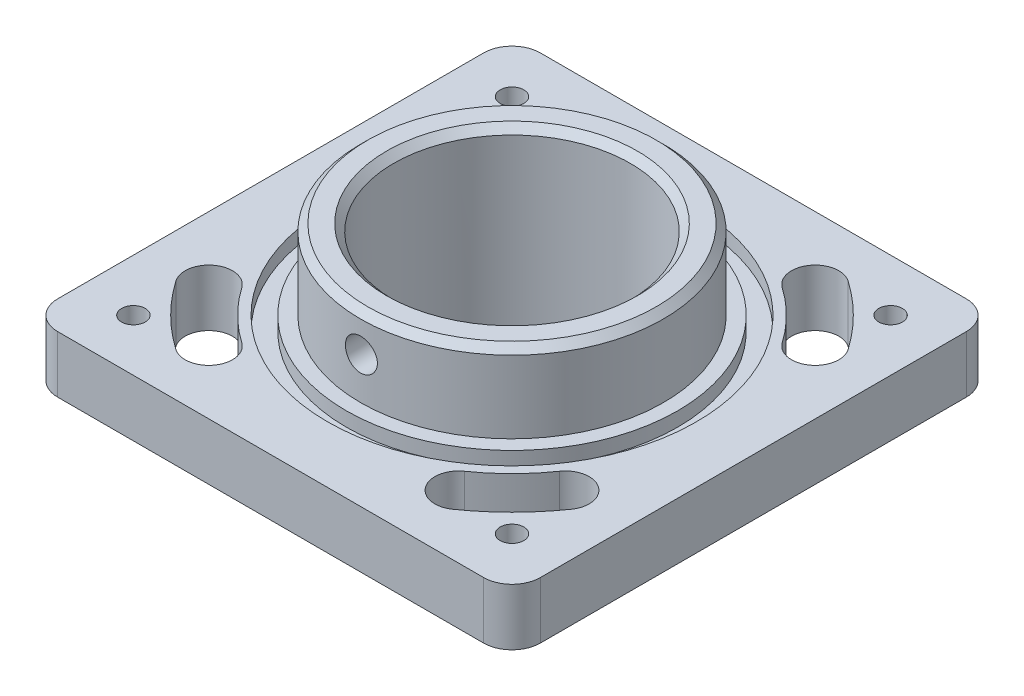
SolidWorks part; units mm, degrees
ref_plane "Face" through (0, 0, 0) normal (0, 0, 1) x (1, 0, 0)
ref_plane "Dessus" through (0, 0, 0) normal (0, 1, 0) x (1, 0, 0)
ref_plane "Droite" through (0, 0, 0) normal (1, 0, 0) x (0, 0, -1)
sketch "Esquisse1" plane through (0, 0, 0) normal (0, 1, 0) x (1, 0, 0)
  line L0 (-59.8186, 41.8854) -> (0, 0) construction
  line L1 (-80.9625, -80.9625) -> (80.9625, -80.9625)
  line L2 (-80.9625, -80.9625) -> (-80.9625, 80.9625)
  line L3 (-80.9625, 80.9625) -> (80.9625, 80.9625)
  line L4 (80.9625, -80.9625) -> (80.9625, 80.9625)
  line L5 (-80.9625, -80.9625) -> (80.9625, 80.9625) construction
  line L6 (-80.9625, 80.9625) -> (80.9625, -80.9625) construction
  line L7 (0, 0) -> (-41.8854, 59.8186) construction
  circle A0 centre (0, 0) radius 39.6875
  arc A1 (-41.8854, 59.8186) -> (-59.8186, 41.8854) centre (0, 0) ccw construction
  arc A2 (-46.4382, 66.3206) -> (-66.3206, 46.4382) centre (0, 0) ccw
  arc A3 (-37.3327, 53.3166) -> (-53.3166, 37.3327) centre (0, 0) ccw
  arc A4 (-37.3327, 53.3166) -> (-46.4382, 66.3206) centre (-41.8854, 59.8186) ccw
  arc A5 (-66.3206, 46.4382) -> (-53.3166, 37.3327) centre (-59.8186, 41.8854) ccw
  arc A6 (59.8186, 41.8854) -> (41.8854, 59.8186) centre (0, 0) ccw construction
  arc A7 (66.3206, 46.4382) -> (46.4382, 66.3206) centre (0, 0) ccw
  arc A8 (53.3166, 37.3327) -> (37.3327, 53.3166) centre (0, 0) ccw
  arc A9 (53.3166, 37.3327) -> (66.3206, 46.4382) centre (59.8186, 41.8854) ccw
  arc A10 (46.4382, 66.3206) -> (37.3327, 53.3166) centre (41.8854, 59.8186) ccw
  arc A11 (41.8854, -59.8186) -> (59.8186, -41.8854) centre (0, 0) ccw construction
  arc A12 (46.4382, -66.3206) -> (66.3206, -46.4382) centre (0, 0) ccw
  arc A13 (37.3327, -53.3166) -> (53.3166, -37.3327) centre (0, 0) ccw
  arc A14 (37.3327, -53.3166) -> (46.4382, -66.3206) centre (41.8854, -59.8186) ccw
  arc A15 (66.3206, -46.4382) -> (53.3166, -37.3327) centre (59.8186, -41.8854) ccw
  arc A16 (-59.8186, -41.8854) -> (-41.8854, -59.8186) centre (0, 0) ccw construction
  arc A17 (-66.3206, -46.4382) -> (-46.4382, -66.3206) centre (0, 0) ccw
  arc A18 (-53.3166, -37.3327) -> (-37.3327, -53.3166) centre (0, 0) ccw
  arc A19 (-53.3166, -37.3327) -> (-66.3206, -46.4382) centre (-59.8186, -41.8854) ccw
  arc A20 (-46.4382, -66.3206) -> (-37.3327, -53.3166) centre (-41.8854, -59.8186) ccw
  point P0 (0, 0)
  point P10 (-51.6365, 51.6365)
  point P23 (51.6365, 51.6365)
  point P30 (51.6365, -51.6365)
  point P37 (-51.6365, -51.6365)
  point P42 (0, 0)
  dimension "D3" = 79.375
  dimension "D6" = 7.9375
  dimension "D1" = 161.925
  dimension "D2" = 161.925
  dimension "D4" = 73.025
  dimension "D5" = 20
  dimension "D7" = 4
extrude "Boss.-Extru.1" add sketch "Esquisse1" against normal blind 19.05
hole_wizard "Trou taraudé 3/8-161" positions "Esquisse2" profile "Esquisse3" tap size "3/8-16" standard "Ansi Inch" end condition through all
sketch "Esquisse2" plane through (0, 0, 0) normal (0, 1, 0) x (1, 0, 0)
  line L0 (80.9625, 80.9625) -> (-80.9625, 80.9625) construction
  line L1 (-80.9625, 80.9625) -> (-80.9625, -80.9625) construction
  point P0 (-63.5, 63.5)
  point P2 (63.5, 63.5)
  point P5 (-63.5, -63.5)
  point P7 (63.5, -63.5)
  dimension "D1" = 127
  dimension "D2" = 127
  dimension "D3" = 17.4625
  dimension "D4" = 17.4625
sketch "Esquisse3" plane through (-63.5, 0, -63.5) normal (1, 0, 0) x (0, 0, 1)
  line L0 (0, 0) -> (0, 19.05)
  line L1 (0, 19.05) -> (3.9687, 19.05)
  line L2 (3.9687, 19.05) -> (3.9687, 0)
  line L5 (3.9687, 0) -> (0, 0)
  line L11 (0, -6.35) -> (0, 107.95) construction
  dimension "Diamètre du trou pour taraudage jusqu'au prochain" = 7.9375
  dimension "Profondeur du trou pour taraudage jusqu'au prochain" = 19.05
cosmetic thread "Filetage de perçage1" parameters "D2"=9.525
cosmetic thread "Filetage de perçage2" parameters "D2"=9.525
cosmetic thread "Filetage de perçage3" parameters "D2"=9.525
cosmetic thread "Filetage de perçage4" parameters "D2"=9.525
sketch "Esquisse4" plane through (0, 0, 0) normal (0, 1, 0) x (1, 0, 0)
  circle A0 centre (0, 0) radius 55.5625
  circle A1 centre (0, 0) radius 61.9125
  dimension "D1" = 111.125
  dimension "D2" = 123.825
extrude "Enlèv. mat.-Extru.1" cut sketch "Esquisse4" against normal blind 4.7625 contours A1 | A0
sketch "Esquisse5" plane through (0, 0, 0) normal (0, 1, 0) x (1, 0, 0)
  circle A0 centre (0, 0) radius 50.8
  circle A1 centre (0, 0) radius 39.6875
  dimension "D1" = 101.6
  dimension "D2" = 79.375
extrude "Boss.-Extru.2" add sketch "Esquisse5" along normal blind 26.67
chamfer "Chanfrein1" [suppressed] distance 2.3813 angle 45
fillet "Congé1" radius 9.525 4 edges at (-80.9625, -9.525, -80.9625) (80.9625, -9.525, -80.9625) (-80.9625, -9.525, 80.9625) (80.9625, -9.525, 80.9625)
ref_plane "Plan1" through (0, 0, 50.8) normal (0, 0, 1) x (1, 0, 0)
hole_wizard "Trou taraudé 1/2-131" positions "Esquisse9" profile "Esquisse10" tap size "1/2-13" standard "Ansi Inch"
sketch "Esquisse9" plane through (0, 0, 50.8) normal (0, 0, 1) x (1, 0, 0)
  line L0 (50.8, 26.67) -> (-50.8, 26.67) construction
  point P0 (0, 13.97)
  point P5 (0, 0)
  dimension "D1" = 12.7
sketch "Esquisse10" plane through (0, 13.97, 50.8) normal (1, 0, 0) x (0, -1, 0)
  line L0 (0, 0) -> (0, 11.1125)
  line L1 (0, 11.1125) -> (5.3581, 11.1125)
  line L2 (5.3581, 11.1125) -> (5.3581, 0)
  line L5 (5.3581, 0) -> (0, 0)
  line L11 (0, -6.35) -> (0, 107.95) construction
  dimension "Diamètre du trou pour taraudage jusqu'au prochain" = 10.7163
  dimension "Profondeur du trou pour taraudage jusqu'au prochain" = 11.1125
cosmetic thread "Filetage de perçage5" parameters "D2"=12.7
chamfer "Chanfrein2" distance 2.3813 angle 45 2 edges at (0, 26.67, 39.6875) (0, 26.67, 50.8)
sketch "Esquisse11" plane through (0, -19.05, 0) normal (0, -1, 0) x (-1, 0, 0)
  circle A0 centre (0, 0) radius 53.975
  circle A2 centre (0, 0) radius 39.6875
  dimension "D1" = 107.95
  dimension "D2" = 79.375
extrude "Boss.-Extru.3" add sketch "Esquisse11" along normal blind 19.05
chamfer "Chanfrein4" distance 2.3813 angle 45 1 edges at (0, -38.1, -39.6875)
